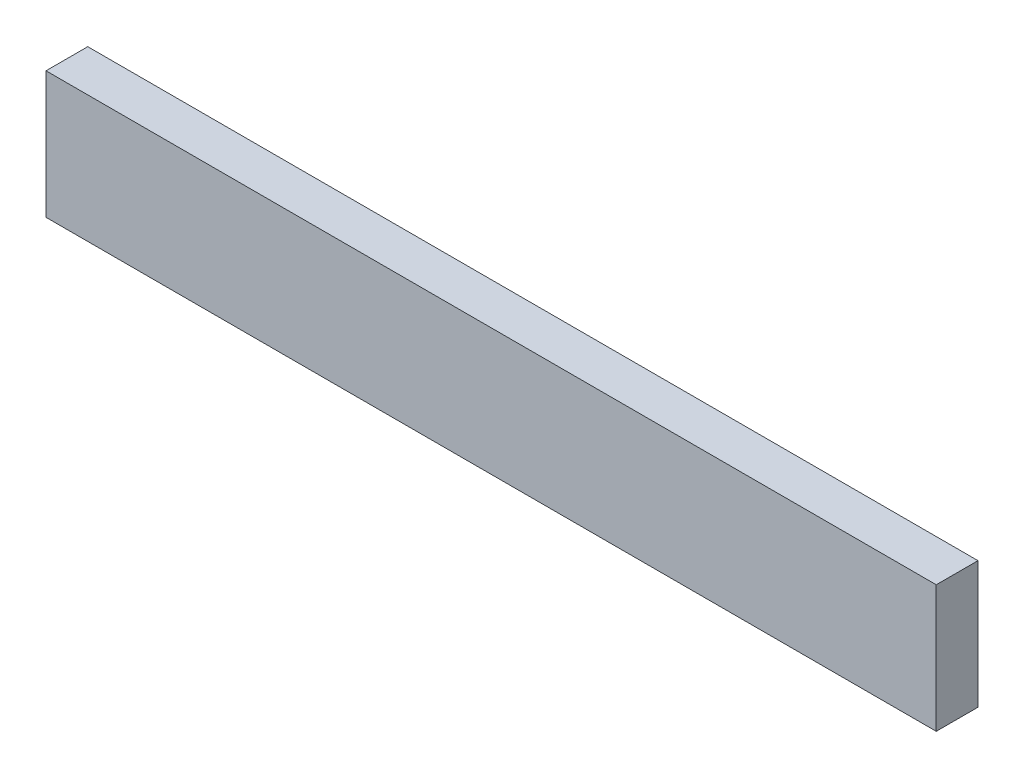
SolidWorks part; units mm, degrees
ref_plane "Front Plane" through (0, 0, 0) normal (0, 0, 1) x (1, 0, 0)
ref_plane "Top Plane" through (0, 0, 0) normal (0, 1, 0) x (1, 0, 0)
ref_plane "Right Plane" through (0, 0, 0) normal (1, 0, 0) x (0, 0, -1)
sketch "Sketch1" plane through (0, 0, 0) normal (0, 0, 1) x (1, 0, 0)
  line L1 (-533, 76) -> (533, 76)
  line L2 (-533, 76) -> (-533, -76)
  line L3 (-533, -76) -> (533, -76)
  line L4 (533, 76) -> (533, -76)
  line L5 (-533, 76) -> (533, -76) construction
  line L6 (-533, -76) -> (533, 76) construction
  point P0 (0, 0)
  dimension "D1" = 1066
  dimension "D2" = 152
extrude "Boss-Extrude1" add sketch "Sketch1" along normal blind 50
